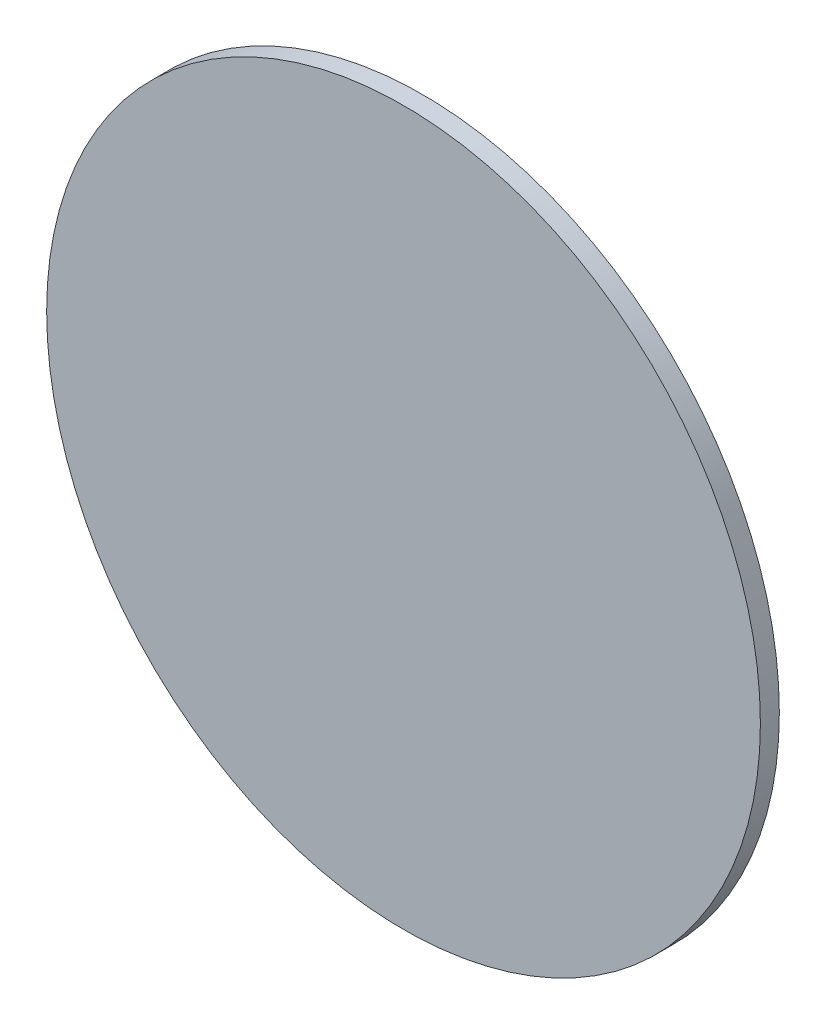
SolidWorks part; units mm, degrees
material "Barium"
ref_plane "Front" through (0, 0, 0) normal (0, 0, 1) x (1, 0, 0)
ref_plane "Top" through (0, 0, 0) normal (0, 1, 0) x (1, 0, 0)
ref_plane "Right" through (0, 0, 0) normal (1, 0, 0) x (0, 0, -1)
sketch "Sketch1" plane through (0, 0, 0) normal (0, 0, 1) x (1, 0, 0)
  circle A0 centre (0, 0) radius 128
extrude "Boss-Extrude1" add sketch "Sketch1" along normal blind 6.8
